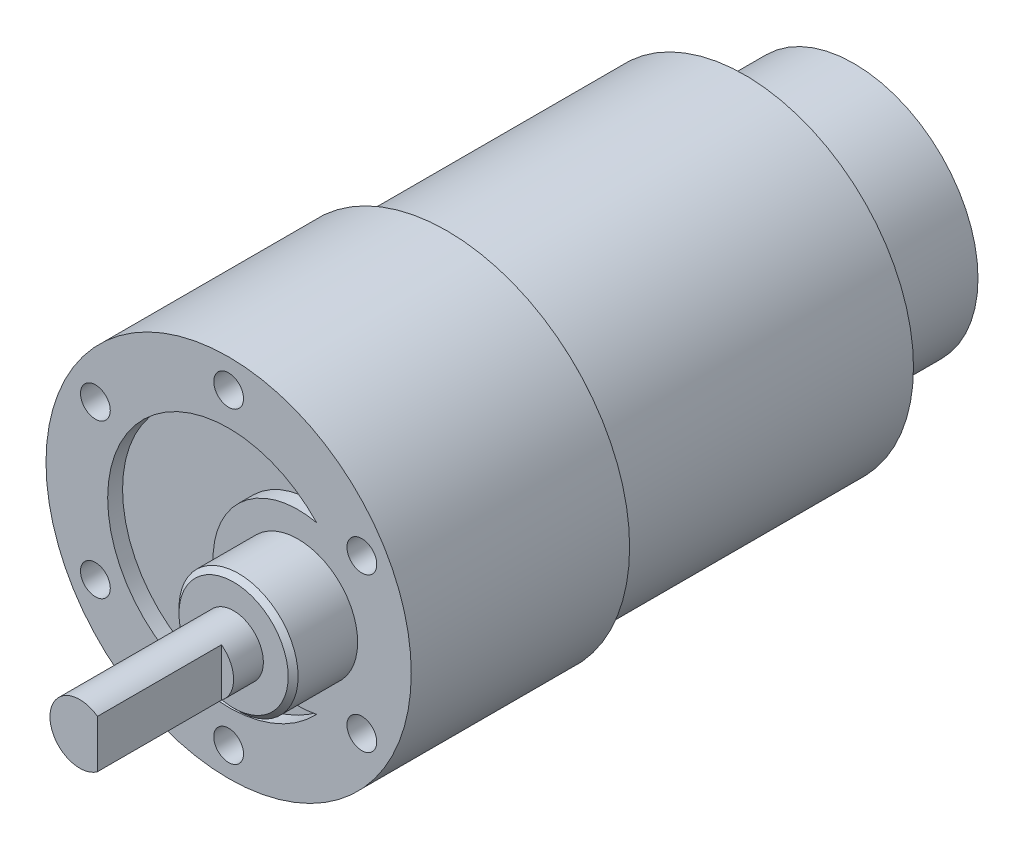
SolidWorks part; units mm, degrees
ref_plane "Front Plane" through (0, 0, 0) normal (0, 0, 1) x (1, 0, 0)
ref_plane "Top Plane" through (0, 0, 0) normal (0, 1, 0) x (1, 0, 0)
ref_plane "Right Plane" through (0, 0, 0) normal (1, 0, 0) x (0, 0, -1)
sketch "Sketch1" plane through (0, 0, 0) normal (0, 0, 1) x (1, 0, 0)
  circle A0 centre (0, 0) radius 17
  dimension "D1" = 34
extrude "Boss-Extrude1" add sketch "Sketch1" along normal blind 30
fillet "Fillet1" radius 1 1 edges at (17, 0, 30)
sketch "Sketch2" plane through (0, 0, 30) normal (0, 0, 1) x (1, 0, 0)
  circle A0 centre (0, 0) radius 18.4
extrude "Boss-Extrude2" add sketch "Sketch2" along normal blind 22
sketch "Sketch3" plane through (0, 0, 52) normal (0, 0, 1) x (1, 0, 0)
  circle A0 centre (0, 15.5) radius 1.5
  circle A1 centre (0, 0) radius 18.4 construction
  circle A2 centre (13.4234, 7.75) radius 1.5
  circle A3 centre (13.4234, -7.75) radius 1.5
  circle A4 centre (0, -15.5) radius 1.5
  circle A5 centre (-13.4234, -7.75) radius 1.5
  circle A6 centre (-13.4234, 7.75) radius 1.5
  dimension "D1" = 15.5
  dimension "D2" = 6
extrude "Cut-Extrude1" cut sketch "Sketch3" against normal blind 3
sketch "Sketch4" plane through (0, 0, 52) normal (0, 0, 1) x (1, 0, 0)
  circle A0 centre (7, 0) radius 6
  circle A1 centre (0, 15.5) radius 1.5 construction
  dimension "D1" = 12
  dimension "D2" = 7
extrude "Boss-Extrude3" add sketch "Sketch4" along normal blind 6.5
chamfer "Chamfer1" distance 0.5 angle 45 1 edges at (13, 0, 58.5)
sketch "Sketch5" plane through (0, 0, 58.5) normal (0, 0, 1) x (1, 0, 0)
  circle A0 centre (7, 0) radius 3
extrude "Boss-Extrude4" add sketch "Sketch5" along normal blind 15.5
sketch "Sketch6" plane through (0, 0, 52) normal (0, 0, 1) x (1, 0, 0)
  circle A0 centre (7, 0) radius 8.5659
  circle A1 centre (0, 0) radius 12.1872
extrude "Cut-Extrude3" cut sketch "Sketch6" against normal blind 1.5 contours A0 A1
sketch "Sketch7" plane through (0, 0, 0) normal (0, 0, -1) x (-1, 0, 0)
  circle A0 centre (0, 0) radius 12.5
  dimension "D1" = 25
extrude "Boss-Extrude5" add sketch "Sketch7" along normal blind 11
sketch "Sketch8" plane through (0, 0, 74) normal (0, 0, 1) x (1, 0, 0)
  line L0 (8.7794, 2.4153) -> (8.7794, -2.4153)
  circle A0 centre (7, 0) radius 3 construction
  arc A1 (8.7794, 2.4153) -> (8.7794, -2.4153) centre (7, 0) cw
extrude "Cut-Extrude4" cut sketch "Sketch8" against normal offset from surface (12.5 mm away) 3 up to face at (12.5, 0, 58.5)
